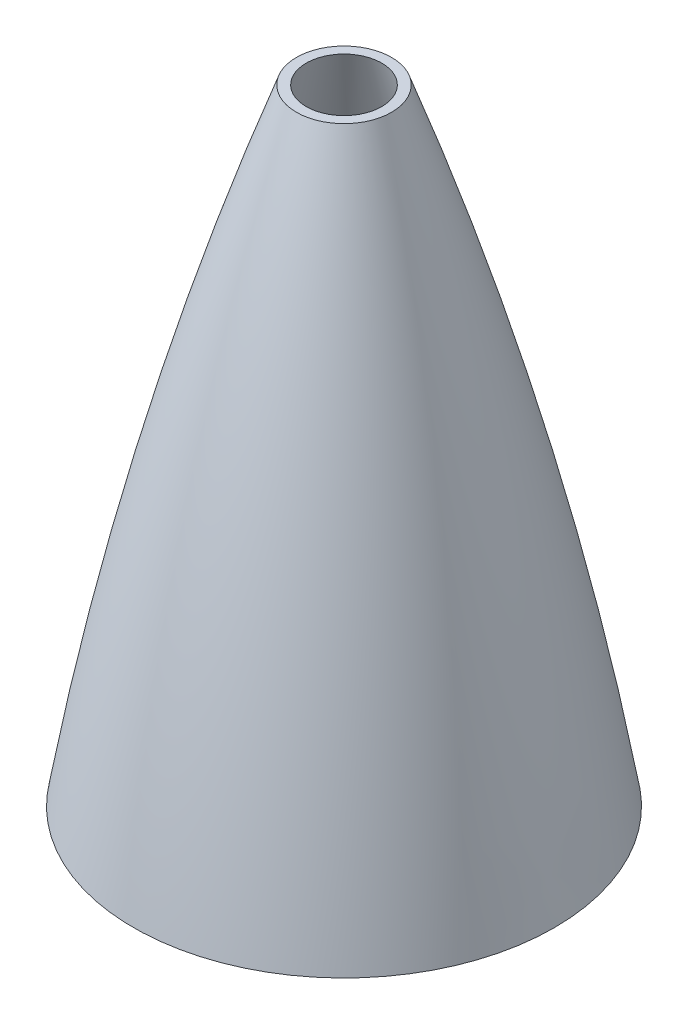
SolidWorks part; units mm, degrees
material "PVB"
ref_plane "Front Plane" through (0, 0, 0) normal (0, 0, 1) x (1, 0, 0)
ref_plane "Top Plane" through (0, 0, 0) normal (0, 1, 0) x (1, 0, 0)
ref_plane "Right Plane" through (0, 0, 0) normal (1, 0, 0) x (0, 0, -1)
sketch "Sketch2" plane through (0, 0, 0) normal (0, 0, 1) x (1, 0, 0)
  line L0 (0, 0) -> (0, 330.2) construction
  line L1 (-76.2, 0) -> (-69.85, 0)
  line L2 (0, 330.2) -> (0, 325.12)
  arc A0 (0, 330.2) -> (-76.2, 0) centre (1014.3906, -77.7824) ccw
  arc A1 (0, 325.12) -> (-69.85, 0) centre (1133.5772, -88.4854) ccw
  dimension "D1" = 330.2
  dimension "D2" = 5.08
  dimension "D3" = 76.2
  dimension "D4" = 6.35
revolve "Revolve1" add sketch "Sketch2" angle 360 about L2
ref_plane "Plane2" through (0, 381, 0) normal (0, 1, 0) x (1, 0, 0)
sketch "Sketch7" plane through (0, 381, 0) normal (0, 1, 0) x (1, 0, 0)
  circle A0 centre (0, 0) radius 317.5
  dimension "D1" = 635
extrude "Cut-Extrude2" cut sketch "Sketch7" against normal blind 88.9
sketch "Sketch8" plane through (0, 0, 0) normal (0, -1, 0) x (1, 0, 0)
  circle A0 centre (0, 0) radius 69.85
  circle A1 centre (0, 0) radius 73.025
  dimension "D1" = 146.05
extrude "Boss-Extrude1" add sketch "Sketch8" along normal blind 76.2
sketch "Sketch9" plane through (0, -76.2, 0) normal (0, -1, 0) x (1, 0, 0)
  circle A0 centre (0, 0) radius 87.2993
extrude "Cut-Extrude3" cut sketch "Sketch9" against normal blind 177.8
